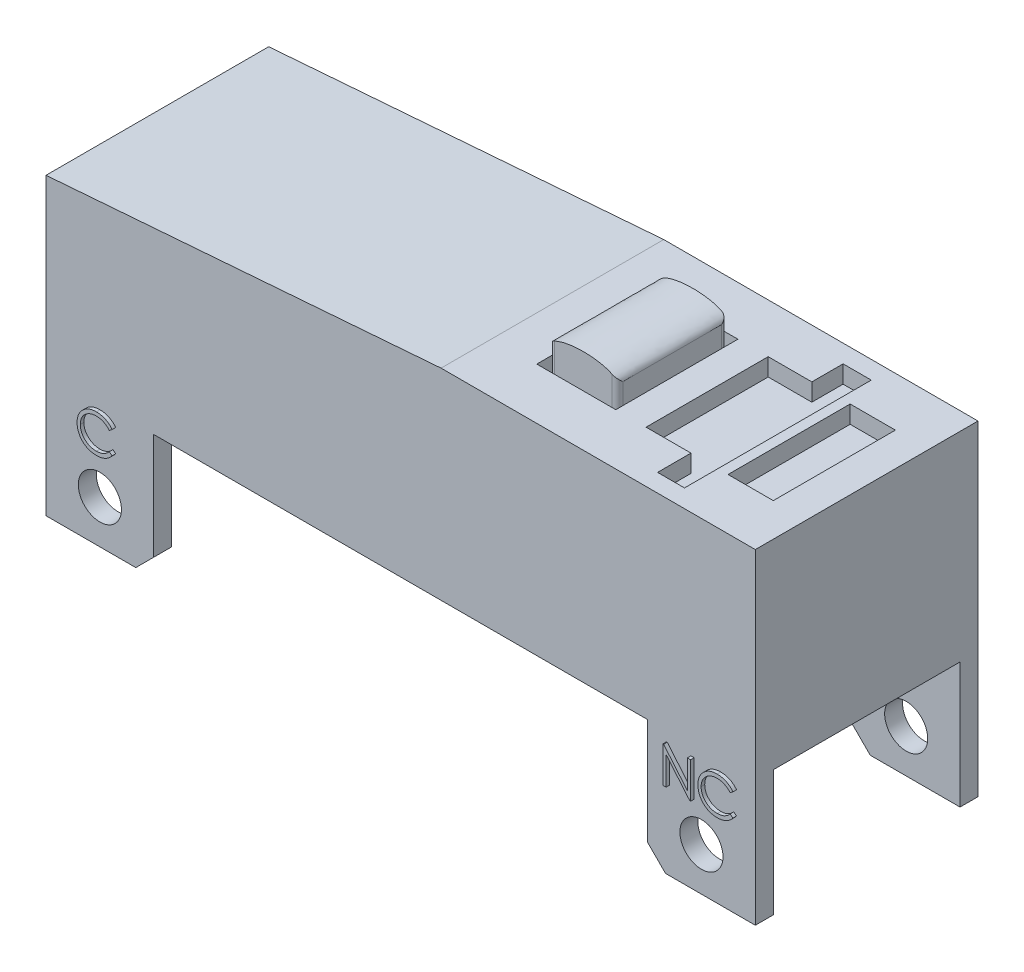
SolidWorks part; units mm, degrees
ref_plane "Front Plane" through (0, 0, 0) normal (0, 0, 1) x (1, 0, 0)
ref_plane "Top Plane" through (0, 0, 0) normal (0, 1, 0) x (1, 0, 0)
ref_plane "Right Plane" through (0, 0, 0) normal (1, 0, 0) x (0, 0, -1)
sketch "Sketch1" plane through (0, 0, 0) normal (0, 0, 1) x (1, 0, 0)
  line L0 (-8.0903, -3.5806) -> (11.6597, -3.5806)
  line L1 (11.6597, -3.5806) -> (11.6597, 6.4194)
  line L2 (11.6597, 6.4194) -> (5.6597, 6.4194)
  line L3 (5.6597, 6.4194) -> (2.9097, 6.4194)
  line L4 (2.9097, 6.4194) -> (-8.0903, 5.5694)
  line L5 (-8.0903, 5.5694) -> (-8.0903, -3.5806)
  line L6 (-9.4849, -12.3806) -> (16.1475, -12.3806) construction
  line L7 (-7.4571, -3.5806) -> (-3.7071, -3.5806)
  line L8 (-7.4571, -3.5806) -> (-7.4571, -5.0806)
  line L9 (-7.4571, -5.0806) -> (-3.7071, -5.0806)
  line L10 (-3.7071, -3.5806) -> (-3.7071, -5.0806)
  line L11 (-0.2345, -3.5806) -> (3.5155, -3.5806)
  line L12 (-0.2345, -3.5806) -> (-0.2345, -5.0806)
  line L13 (-0.2345, -5.0806) -> (3.5155, -5.0806)
  line L14 (3.5155, -3.5806) -> (3.5155, -5.0806)
  line L15 (11.1929, -3.5806) -> (7.4429, -3.5806)
  line L16 (11.1929, -3.5806) -> (11.1929, -5.0806)
  line L17 (11.1929, -5.0806) -> (7.4429, -5.0806)
  line L18 (7.4429, -3.5806) -> (7.4429, -5.0806)
  line L19 (-2.7403, -3.5806) -> (-1.9103, -3.5806)
  line L20 (-2.7403, -3.5806) -> (-2.7403, -4.5806)
  line L21 (-2.7403, -4.5806) -> (-1.9103, -4.5806)
  line L22 (-1.9103, -3.5806) -> (-1.9103, -4.5806)
  line L23 (5.4797, -3.5806) -> (6.3097, -3.5806)
  line L24 (5.4797, -3.5806) -> (5.4797, -4.5806)
  line L25 (5.4797, -4.5806) -> (6.3097, -4.5806)
  line L26 (6.3097, -3.5806) -> (6.3097, -4.5806)
  line L27 (1.7847, -3.1806) -> (1.7847, 19.2367) construction
  line L28 (10.8929, -5.0806) -> (8.0929, -5.0806)
  line L29 (10.8929, -5.0806) -> (10.8929, -12.3806)
  line L30 (10.8929, -12.3806) -> (8.0929, -12.3806)
  line L31 (8.0929, -5.0806) -> (8.0929, -12.3806)
  line L32 (3.5155, -5.0806) -> (0.7155, -5.0806)
  line L33 (3.5155, -5.0806) -> (3.5155, -12.3806)
  line L34 (3.5155, -12.3806) -> (0.7155, -12.3806)
  line L35 (0.7155, -5.0806) -> (0.7155, -12.3806)
  line L36 (-7.1571, -5.0806) -> (-4.3571, -5.0806)
  line L37 (-7.1571, -5.0806) -> (-7.1571, -12.3806)
  line L38 (-7.1571, -12.3806) -> (-4.3571, -12.3806)
  line L39 (-4.3571, -5.0806) -> (-4.3571, -12.3806)
  line L40 (-8.0903, -3.1806) -> (11.6597, -3.1806)
  line L41 (-8.0903, -3.1806) -> (-8.0903, -3.5806)
  line L42 (-8.0903, -3.5806) -> (11.6597, -3.5806)
  line L43 (11.6597, -3.1806) -> (11.6597, -3.5806)
  line L44 (-8.0903, -2.6406) -> (-5.0903, -2.6406)
  line L45 (-5.0903, 0.8194) -> (-5.0903, -2.6406)
  line L46 (-5.0903, 0.8194) -> (8.6597, 0.8194)
  line L47 (8.6597, 0.8194) -> (8.6597, -2.6406)
  line L48 (8.6597, -2.6406) -> (11.6597, -2.6406)
  dimension "D1" = 10
  dimension "D2" = 19.75
  dimension "D3" = 9.15
  dimension "D5" = 6
  dimension "D4" = 11
  dimension "D6" = 18.65
  dimension "D7" = 3.75
  dimension "D8" = 3.75
  dimension "D9" = 3.75
  dimension "D10" = 5.35
  dimension "D11" = 5.35
  dimension "D12" = 0.83
  dimension "D13" = 0.83
  dimension "D14" = 1
  dimension "D15" = 1
  dimension "D16" = 1.5
  dimension "D17" = 8.8
  dimension "D18" = 2.8
  dimension "D19" = 2.8
  dimension "D20" = 2.8
  dimension "D21" = 0.3
  dimension "D22" = 0.3
  dimension "D23" = 0.4
  dimension "D26" = 0.54
  dimension "D27" = 19.75
  dimension "D24" = 13.75
  dimension "D25" = 6.875
  dimension "D28" = 3.46
sketch "Sketch2" plane through (0, 0, 0) normal (0, 0, 1) x (1, 0, 0)
  line L0 (-8.0903, -3.5806) -> (11.6597, -3.5806)
  line L1 (11.6597, -3.5806) -> (11.6597, 6.4194)
  line L2 (11.6597, 6.4194) -> (5.6597, 6.4194)
  line L3 (5.6597, 6.4194) -> (2.9097, 6.4194)
  line L4 (2.9097, 6.4194) -> (-8.0903, 5.5694)
  line L5 (-8.0903, 5.5694) -> (-8.0903, -3.5806)
  line L6 (-9.4849, -12.3806) -> (16.1475, -12.3806) construction
  line L7 (-7.4571, -3.5806) -> (-3.7071, -3.5806)
  line L8 (-7.4571, -3.5806) -> (-7.4571, -5.0806)
  line L9 (-7.4571, -5.0806) -> (-3.7071, -5.0806)
  line L10 (-3.7071, -3.5806) -> (-3.7071, -5.0806)
  line L11 (-0.2345, -3.5806) -> (3.5155, -3.5806)
  line L12 (-0.2345, -3.5806) -> (-0.2345, -5.0806)
  line L13 (-0.2345, -5.0806) -> (3.5155, -5.0806)
  line L14 (3.5155, -3.5806) -> (3.5155, -5.0806)
  line L15 (11.1929, -3.5806) -> (7.4429, -3.5806)
  line L16 (11.1929, -3.5806) -> (11.1929, -5.0806)
  line L17 (11.1929, -5.0806) -> (7.4429, -5.0806)
  line L18 (7.4429, -3.5806) -> (7.4429, -5.0806)
  line L19 (-2.7403, -3.5806) -> (-1.9103, -3.5806)
  line L20 (-2.7403, -3.5806) -> (-2.7403, -4.5806)
  line L21 (-2.7403, -4.5806) -> (-1.9103, -4.5806)
  line L22 (-1.9103, -3.5806) -> (-1.9103, -4.5806)
  line L23 (5.4797, -3.5806) -> (6.3097, -3.5806)
  line L24 (5.4797, -3.5806) -> (5.4797, -4.5806)
  line L25 (5.4797, -4.5806) -> (6.3097, -4.5806)
  line L26 (6.3097, -3.5806) -> (6.3097, -4.5806)
  line L27 (1.7847, -3.1806) -> (1.7847, 19.2367) construction
  line L28 (10.8929, -5.0806) -> (8.0929, -5.0806)
  line L29 (10.8929, -5.0806) -> (10.8929, -12.3806)
  line L30 (10.8929, -12.3806) -> (8.0929, -12.3806)
  line L31 (8.0929, -5.0806) -> (8.0929, -12.3806)
  line L32 (3.5155, -5.0806) -> (0.7155, -5.0806)
  line L33 (3.5155, -5.0806) -> (3.5155, -12.3806)
  line L34 (3.5155, -12.3806) -> (0.7155, -12.3806)
  line L35 (0.7155, -5.0806) -> (0.7155, -12.3806)
  line L36 (-7.1571, -5.0806) -> (-4.3571, -5.0806)
  line L37 (-7.1571, -5.0806) -> (-7.1571, -12.3806)
  line L38 (-7.1571, -12.3806) -> (-4.3571, -12.3806)
  line L39 (-4.3571, -5.0806) -> (-4.3571, -12.3806)
  line L40 (-8.0903, -3.1806) -> (11.6597, -3.1806)
  line L41 (-8.0903, -3.1806) -> (-8.0903, -3.5806)
  line L42 (-8.0903, -3.5806) -> (11.6597, -3.5806)
  line L43 (11.6597, -3.1806) -> (11.6597, -3.5806)
  line L44 (-8.0903, -2.6406) -> (-5.0903, -2.6406)
  line L45 (-5.0903, 0.8194) -> (-5.0903, -2.6406)
  line L46 (-5.0903, 0.8194) -> (8.6597, 0.8194)
  line L47 (8.6597, 0.8194) -> (8.6597, -2.6406)
  line L48 (8.6597, -2.6406) -> (11.6597, -2.6406)
  dimension "D1" = 10
  dimension "D2" = 19.75
  dimension "D3" = 9.15
  dimension "D4" = 11
  dimension "D5" = 6
  dimension "D6" = 18.65
  dimension "D7" = 3.75
  dimension "D8" = 3.75
  dimension "D9" = 3.75
  dimension "D10" = 5.35
  dimension "D11" = 5.35
  dimension "D12" = 0.83
  dimension "D13" = 0.83
  dimension "D14" = 1
  dimension "D15" = 1
  dimension "D16" = 1.5
  dimension "D17" = 8.8
  dimension "D18" = 2.8
  dimension "D19" = 2.8
  dimension "D20" = 2.8
  dimension "D21" = 0.3
  dimension "D22" = 0.3
  dimension "D23" = 0.4
  dimension "D24" = 13.75
  dimension "D25" = 6.875
  dimension "D26" = 0.54
  dimension "D27" = 19.75
  dimension "D28" = 3.46
sketch "Sketch3" plane through (0, 0, 0) normal (0, 0, 1) x (1, 0, 0)
  line L2 (11.6597, 6.4194) -> (5.6597, 6.4194)
  line L3 (5.6597, 6.4194) -> (2.9097, 6.4194)
  line L4 (2.9097, 6.4194) -> (-8.0903, 5.5694)
  line L6 (-8.0903, 5.5694) -> (-8.0903, -2.6406)
  line L27 (11.6597, -2.6406) -> (11.6597, 6.4194)
  line L44 (-8.0903, -2.6406) -> (-5.5903, -2.6406)
  line L45 (-5.0903, 0.8194) -> (-5.0903, -2.1406)
  line L46 (-5.0903, 0.8194) -> (8.6597, 0.8194)
  line L47 (8.6597, 0.8194) -> (8.6597, -2.1406)
  line L48 (9.1597, -2.6406) -> (11.6597, -2.6406)
  line L49 (-5.0903, -2.1406) -> (-5.5903, -2.6406)
  line L50 (8.6597, -2.1406) -> (9.1597, -2.6406)
  circle A0 centre (-6.5903, -1.4406) radius 0.6
  circle A1 centre (10.1597, -1.4406) radius 0.6
  point P44 (-5.0903, -2.6406)
  point P50 (8.6597, -2.6406)
  dimension "D4" = 11
  dimension "D24" = 13.75
  dimension "D11" = 1.2
  dimension "D15" = 1.2
  dimension "D1" = 2.75
  dimension "D3" = 6
  dimension "D5" = 2.9097
  dimension "D6" = 8.6597
  dimension "D7" = 0.8194
  dimension "D8" = 5.5694
  dimension "D9" = 6.4194
  dimension "D10" = 2.6406
  dimension "D12" = 3
  dimension "D13" = 1.5
  dimension "D14" = 1.2
  dimension "D16" = 1.2
  dimension "D17" = 3
  dimension "D18" = 1.5
sketch "Sketch4" plane through (0, 0, 0) normal (0, 0, 1) x (1, 0, 0)
  line L0 (-8.0903, -3.5806) -> (11.6597, -3.5806)
  line L5 (-8.0903, 5.5694) -> (-8.0903, -3.5806)
  line L6 (-9.4849, -12.3806) -> (16.1475, -12.3806) construction
  line L7 (-7.4571, -3.5806) -> (-3.7071, -3.5806)
  line L8 (-7.4571, -3.5806) -> (-7.4571, -5.0806)
  line L9 (-7.4571, -5.0806) -> (-7.1571, -5.0806)
  line L10 (-3.7071, -3.5806) -> (-3.7071, -5.0806)
  line L11 (-0.2345, -3.5806) -> (3.5155, -3.5806)
  line L12 (-0.2345, -3.5806) -> (-0.2345, -5.0806)
  line L13 (-0.2345, -5.0806) -> (0.7155, -5.0806)
  line L14 (3.5155, -3.5806) -> (3.5155, -5.0806)
  line L15 (11.1929, -3.5806) -> (7.4429, -3.5806)
  line L16 (11.1929, -3.5806) -> (11.1929, -5.0806)
  line L17 (11.1929, -5.0806) -> (10.8929, -5.0806)
  line L18 (7.4429, -3.5806) -> (7.4429, -5.0806)
  line L19 (-2.7403, -3.5806) -> (-1.9103, -3.5806)
  line L20 (-2.7403, -3.5806) -> (-2.7403, -4.5806)
  line L21 (-2.7403, -4.5806) -> (-1.9103, -4.5806)
  line L22 (-1.9103, -3.5806) -> (-1.9103, -4.5806)
  line L23 (5.4797, -3.5806) -> (6.3097, -3.5806)
  line L24 (5.4797, -3.5806) -> (5.4797, -4.5806)
  line L25 (5.4797, -4.5806) -> (6.3097, -4.5806)
  line L26 (6.3097, -3.5806) -> (6.3097, -4.5806)
  line L27 (1.7847, -3.1806) -> (1.7847, 19.2367) construction
  line L29 (10.8929, -5.0806) -> (10.8929, -11.7806)
  line L30 (10.2929, -12.3806) -> (8.6929, -12.3806)
  line L31 (8.0929, -5.0806) -> (8.0929, -11.7806)
  line L33 (3.5155, -5.0806) -> (3.5155, -11.7806)
  line L34 (2.9155, -12.3806) -> (1.3155, -12.3806)
  line L35 (0.7155, -5.0806) -> (0.7155, -11.7806)
  line L37 (-7.1571, -5.0806) -> (-7.1571, -11.7806)
  line L38 (-6.5571, -12.3806) -> (-4.9571, -12.3806)
  line L39 (-4.3571, -5.0806) -> (-4.3571, -11.7806)
  line L40 (-8.0903, -3.1806) -> (11.6597, -3.1806)
  line L41 (-8.0903, -3.1806) -> (-8.0903, -3.5806)
  line L42 (-8.0903, -3.5806) -> (11.6597, -3.5806)
  line L43 (11.6597, -3.1806) -> (11.6597, -3.5806)
  line L44 (-8.0903, -2.6406) -> (-5.0903, -2.6406)
  line L45 (-5.0903, 0.8194) -> (-5.0903, -2.6406)
  line L46 (-5.0903, 0.8194) -> (8.6597, 0.8194)
  line L47 (8.6597, 0.8194) -> (8.6597, -2.6406)
  line L48 (8.6597, -2.6406) -> (11.6597, -2.6406)
  line L49 (-4.3571, -5.0806) -> (-3.7071, -5.0806)
  line L50 (8.0929, -5.0806) -> (7.4429, -5.0806)
  line L51 (-7.1571, -11.7806) -> (-6.5571, -12.3806)
  line L52 (-4.9571, -12.3806) -> (-4.3571, -11.7806)
  line L53 (1.3155, -12.3806) -> (0.7155, -11.7806)
  line L54 (3.5155, -11.7806) -> (2.9155, -12.3806)
  line L55 (8.6929, -12.3806) -> (8.0929, -11.7806)
  line L56 (10.8929, -11.7806) -> (10.2929, -12.3806)
  circle A0 centre (2.1155, -11.0806) radius 0.5969
  circle A1 centre (-5.7571, -11.0806) radius 0.5969
  circle A2 centre (9.4929, -11.0806) radius 0.5969
  point P29 (8.0929, -12.3806)
  point P30 (10.8929, -12.3806)
  point P32 (0.7155, -12.3806)
  point P33 (3.5155, -12.3806)
  point P36 (-4.3571, -12.3806)
  point P37 (-7.1571, -12.3806)
  dimension "D2" = 19.75
  dimension "D3" = 9.15
  dimension "D6" = 18.65
  dimension "D7" = 3.75
  dimension "D8" = 3.75
  dimension "D9" = 3.75
  dimension "D10" = 5.35
  dimension "D12" = 0.83
  dimension "D13" = 0.83
  dimension "D14" = 1
  dimension "D15" = 1
  dimension "D16" = 1.5
  dimension "D17" = 8.8
  dimension "D18" = 2.8
  dimension "D19" = 2.8
  dimension "D20" = 2.8
  dimension "D21" = 0.3
  dimension "D22" = 0.3
  dimension "D23" = 0.4
  dimension "D26" = 0.54
  dimension "D25" = 6.875
  dimension "D28" = 3.46
  dimension "D29" = 1.1938
  dimension "D32" = 1.1938
  dimension "D33" = 1.1938
  dimension "D30" = 1.4
  dimension "D31" = 1.3
  dimension "D34" = 1.4
  dimension "D35" = 1.4
extrude "Boss-Extrude1" add sketch "Sketch3" along normal blind 6.2
shell "Shell1" thickness 0.5
sketch "Sketch5" plane through (11.6597, 0, 0) normal (1, 0, 0) x (0, 0, -1)
  line L0 (-6.2, -2.6406) -> (-6.2, 6.4194) construction
  line L1 (-5.7, 0.8594) -> (-0.5, 0.8594)
  line L2 (-5.7, 0.8594) -> (-5.7, -2.6406)
  line L3 (-5.7, -2.6406) -> (-0.5, -2.6406)
  line L4 (-0.5, 0.8594) -> (-0.5, -2.6406)
  line L5 (0, -2.6406) -> (0, 6.4194) construction
  dimension "D1" = 0.5
  dimension "D2" = 0.5
  dimension "D3" = 3.5
  dimension "D4" = 5.2
  dimension "D5" = 3.5
  dimension "D6" = 5.2
extrude "Cut-Extrude1" cut sketch "Sketch5" against normal through all both and the other way through all
sketch "Sketch6" plane through (0, 6.4194, 0) normal (0, 1, 0) x (1, 0, 0)
  line L0 (11.6597, -6.2) -> (11.6597, 0) construction
  line L1 (10.7297, -1.37) -> (9.4697, -1.37)
  line L2 (10.7297, -1.37) -> (10.7297, -4.77)
  line L3 (10.7297, -4.77) -> (9.4697, -4.77)
  line L4 (9.4697, -1.37) -> (9.4697, -4.77)
  line L5 (11.6597, 0) -> (2.9097, 0) construction
  point P6 (10.7297, -3.07)
  dimension "D1" = 0.93
  dimension "D2" = 1.26
  dimension "D3" = 3.4
  dimension "D4" = 3.07
extrude "Cut-Extrude2" cut sketch "Sketch6" against normal blind 0.49
sketch "Sketch7" plane through (0, 6.4194, 0) normal (0, 1, 0) x (1, 0, 0)
  line L0 (9.1878, -0.5) -> (9.1878, -5.7)
  line L1 (9.1878, -5.7) -> (8.4378, -5.7)
  line L2 (8.4378, -5.7) -> (8.4378, -4.77)
  line L3 (8.4378, -4.77) -> (7.1878, -4.77)
  line L4 (7.1878, -4.77) -> (7.1878, -1.37)
  line L5 (7.1878, -1.37) -> (8.403, -1.37)
  line L6 (8.403, -1.37) -> (8.403, -0.5)
  line L7 (8.403, -0.5) -> (9.1878, -0.5)
  line L9 (6.3448, -1.37) -> (4.1448, -1.37)
  line L10 (6.3448, -1.37) -> (6.3448, -4.77)
  line L11 (6.3448, -4.77) -> (4.1448, -4.77)
  line L12 (4.1448, -1.37) -> (4.1448, -4.77)
  line L17 (10.7297, -4.77) -> (10.7297, -1.37) construction
  line L18 (9.4697, -4.77) -> (10.7297, -4.77) construction
  dimension "D1" = 1.5419
  dimension "D2" = 2.2919
  dimension "D3" = 2.3267
  dimension "D4" = 3.5419
  dimension "D5" = 4.3849
  dimension "D6" = 6.5849
  dimension "D7" = 3.4
  dimension "D8" = 4.27
  dimension "D9" = 0.93
extrude "Cut-Extrude3" cut sketch "Sketch7" against normal blind 0.49
sketch "Sketch8" plane through (0, 5.9294, 0) normal (0, 1, 0) x (1, 0, 0)
  line L0 (6.3448, -1.37) -> (4.1448, -1.37) construction
  line L1 (4.4448, -1.52) -> (6.0448, -1.52)
  line L2 (4.2948, -1.67) -> (4.2948, -4.42)
  line L3 (4.4448, -4.57) -> (6.0448, -4.57)
  line L4 (6.1948, -1.67) -> (6.1948, -4.42)
  line L5 (4.1448, -4.77) -> (6.3448, -4.77) construction
  line L6 (4.1448, -1.37) -> (4.1448, -4.77) construction
  line L7 (6.3448, -4.77) -> (6.3448, -1.37) construction
  arc A0 (6.0448, -1.52) -> (6.1948, -1.67) centre (6.0448, -1.67) cw
  arc A1 (6.0448, -4.57) -> (6.1948, -4.42) centre (6.0448, -4.42) ccw
  arc A2 (4.2948, -4.42) -> (4.4448, -4.57) centre (4.4448, -4.42) ccw
  arc A3 (4.4448, -1.52) -> (4.2948, -1.67) centre (4.4448, -1.67) ccw
  dimension "D5" = 0.15
  dimension "D1" = 0.15
  dimension "D2" = 0.2
  dimension "D3" = 0.15
  dimension "D4" = 0.15
extrude "Boss-Extrude2" add sketch "Sketch8" along normal blind 1.24
sketch "Sketch9" plane through (0, 0, 4.57) normal (0, 0, 1) x (1, 0, 0)
  line L2 (4.4448, 7.1694) -> (6.0448, 7.1694) construction
  line L3 (4.2948, 6.8476) -> (4.2948, 7.1694)
  line L4 (4.2948, 7.1694) -> (6.1948, 7.1694)
  line L5 (6.1948, 7.1694) -> (6.1948, 6.8476)
  line L8 (4.4448, 5.9294) -> (6.0448, 5.9294) construction
  ellipse E0 centre (5.2448, 6.8476) end of major axis (4.2948, 6.8476) minor radius 0.3218 (6.1948, 6.8476) -> (4.2948, 6.8476) ccw
  line M3 (6.0448, 5.9294) -> (6.0448, 7.1694)
  line M4 (6.0448, 7.1694) -> (4.4448, 7.1694)
  line M5 (4.4448, 7.1694) -> (4.4448, 5.9294)
  dimension "D1" = 0.5964
extrude "Cut-Extrude4" cut sketch "Sketch9" against normal through all both and the other way through all contours E0 L4 L3 M5 | E0 L4 M5 | E0 M3 M4 | E0 L5 L4 M3
sketch "Sketch10" plane through (4.2948, 0, 0) normal (-1, 0, 0) x (0, 0, 1)
  line L0 (4.57, 7.1694) -> (1.52, 7.1694) construction
  line L2 (1.52, 6.9709) -> (1.52, 7.1694)
  line L3 (1.52, 7.1694) -> (4.57, 7.1694)
  line L4 (4.57, 7.1694) -> (4.57, 6.9709)
  line L5 (1.67, 6.8476) -> (4.42, 6.8476) construction
  ellipse E0 centre (3.045, 6.9709) end of major axis (1.52, 6.9709) minor radius 0.1985 (4.57, 6.9709) -> (1.52, 6.9709) ccw
  dimension "D1" = 0.1233
extrude "Cut-Extrude5" [suppressed] cut sketch "Sketch10" against normal through all both and the other way through all contours E0 L3 L2 | E0 L4 L3
sketch "Sketch11" plane through (0, 0, 6.2) normal (0, 0, 1) x (1, 0, 0)
  line L0 (-8.0903, 5.5694) -> (-8.0903, -2.6406) construction
  line L1 (-8.0903, -2.6406) -> (-5.5903, -2.6406) construction
  text T0 "NC" font "Century Gothic" height 1
  text T1 "C" font "Century Gothic" height 1
  dimension "D1" = 0.8885
  dimension "D2" = 17.149
  dimension "D3" = 2.1892
  dimension "D4" = 2.2815
extrude "Boss-Extrude3" add sketch "Sketch11" along normal blind 0.1
equation "\"D19@Sketch1\"=\"D18@Sketch1\""
equation "\"D20@Sketch1\"=\"D18@Sketch1\""
equation "\"D25@Sketch1\"=\"D24@Sketch1\"/2"
equation "\"D28@Sketch1\"=4-\"D26@Sketch1\""
equation "\"D30@Sketch4\"=\"D19@Sketch4\"/2"
equation "\"D32@Sketch4\"=\"D29@Sketch4\""
equation "\"D33@Sketch4\"=\"D29@Sketch4\""
equation "\"D34@Sketch4\"=\"D30@Sketch4\""
equation "\"D35@Sketch4\"=\"D30@Sketch4\""
equation "\"D13@Sketch3\"=\"D12@Sketch3\"/2"
equation "\"D15@Sketch3\"=\"D11@Sketch3\""
equation "\"D18@Sketch3\"=\"D17@Sketch3\"/2"
